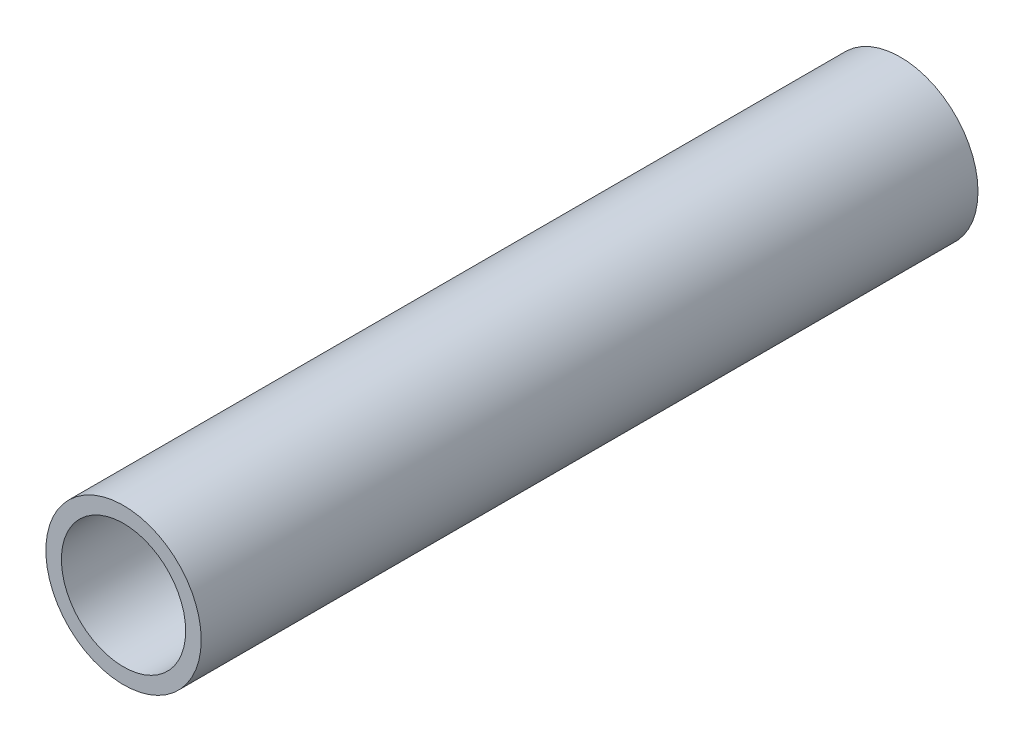
SolidWorks part; units mm, degrees
material "PVC Rigid"
ref_plane "Front Plane" through (0, 0, 0) normal (0, 0, 1) x (1, 0, 0)
ref_plane "Top Plane" through (0, 0, 0) normal (0, 1, 0) x (1, 0, 0)
ref_plane "Right Plane" through (0, 0, 0) normal (1, 0, 0) x (0, 0, -1)
sketch "Sketch1" plane through (0, 0, 0) normal (0, 0, 1) x (1, 0, 0)
  circle A0 centre (0, 0) radius 12.7
  circle A1 centre (0, 0) radius 10.16
  dimension "D1" = 25.4
  dimension "D2" = 20.32
extrude "Boss-Extrude1" add sketch "Sketch1" along normal blind 127
